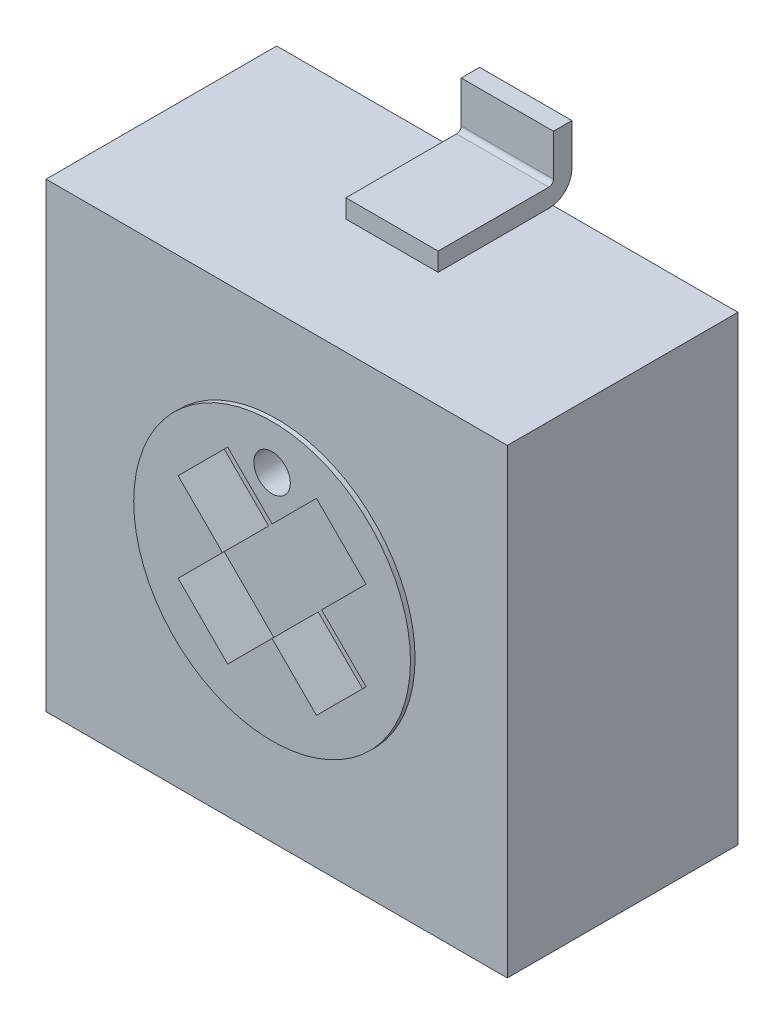
SolidWorks part; units mm, degrees
ref_plane "Front Plane" through (0, 0, 0) normal (0, 0, 1) x (1, 0, 0)
ref_plane "Top Plane" through (0, 0, 0) normal (0, 1, 0) x (1, 0, 0)
ref_plane "Right Plane" through (0, 0, 0) normal (1, 0, 0) x (0, 0, -1)
sketch "Sketch1" plane through (0, 0, 0) normal (0, 0, 1) x (1, 0, 0)
  line L1 (0, 0) -> (5, 0)
  line L2 (0, 0) -> (0, 5)
  line L3 (0, 5) -> (5, 5)
  line L4 (5, 0) -> (5, 5)
  dimension "D1" = 5
  dimension "D2" = 5
extrude "Boss-Extrude1" add sketch "Sketch1" along normal blind 2.5
ref_plane "Plane1" through (2.5, 0, 0) normal (1, 0, 0) x (0, 0, -1)
ref_plane "Plane2" through (1.35, 0, 0) normal (1, 0, 0) x (0, 0, -1)
sketch "Sketch2" plane through (2.5, 0, 0) normal (1, 0, 0) x (0, 0, -1)
  line L0 (-1.25, 5) -> (0.2, 5)
  line L1 (-2.5, 5) -> (0, 5) construction
  line L2 (0.2, 5) -> (0.2, 5.7)
  line L3 (-2.5, 0) -> (-2.5, 5) construction
  dimension "D1" = 2.7
  dimension "D2" = 0.7
extrude "Extrude-Thin1" add sketch "Sketch2" along normal mid plane 1 thin thin type one direction reverse wall 0.2
sketch "Sketch3" plane through (1.35, 0, 0) normal (1, 0, 0) x (0, 0, -1)
  line L0 (-1.25, 0) -> (0.2, 0)
  line L1 (-2.5, 0) -> (0, 0) construction
  line L2 (0.2, 0) -> (0.2, -0.7)
  line L3 (-2.5, 0) -> (-2.5, 5) construction
  dimension "D1" = 2.7
  dimension "D2" = 0.7
extrude "Extrude-Thin2" add sketch "Sketch3" along normal mid plane 0.9 thin
pattern_linear "LPattern1" count 2 spacing 2.3 along (1, 0, 0) of "Extrude-Thin2"
sketch "Sketch4" plane through (0, 0, 2.5) normal (0, 0, 1) x (1, 0, 0)
  circle A0 centre (2.5, 2.5) radius 1.5
  dimension "D1" = 3
extrude "Boss-Extrude2" add sketch "Sketch4" along normal blind 0.05
sketch "Sketch5" plane through (0, 0, 2.55) normal (0, 0, 1) x (1, 0, 0)
  line L0 (1, 2.5) -> (4, 2.5) construction
  line L1 (4, 2.5) -> (2.5, 4) construction
  line L2 (2.5, 4) -> (2.5, 1) construction
  line L3 (2.5, 1) -> (4, 2.5) construction
  line L4 (3.5607, 1.4393) -> (1.4393, 3.5607) construction
  line L5 (2.5, 4) -> (1, 2.5) construction
  line L6 (3.5607, 3.5607) -> (1.4393, 1.4393) construction
  line L7 (1, 2.5) -> (2.5, 1) construction
  line L8 (1.75, 3.25) -> (3.25, 1.75) construction
  line L9 (2.0187, 3.5187) -> (2.5, 3.0374)
  line L10 (3.25, 3.25) -> (1.75, 1.75) construction
  line L11 (1.75, 3.25) -> (3.25, 1.75) construction
  line L12 (1.4813, 2.9813) -> (1.9626, 2.5)
  line L13 (3.5187, 2.9813) -> (3.0374, 2.5)
  line L14 (3.25, 3.25) -> (1.75, 1.75) construction
  line L15 (2.9813, 3.5187) -> (2.5, 3.0374)
  line L16 (2.9813, 3.5187) -> (3.5187, 2.9813)
  line L17 (3.5187, 2.0187) -> (2.9813, 1.4813)
  line L18 (2.0187, 1.4813) -> (1.4813, 2.0187)
  line L19 (1.4813, 2.9813) -> (2.0187, 3.5187)
  line L20 (1.9626, 2.5) -> (1.4813, 2.0187)
  line L21 (3.0374, 2.5) -> (3.5187, 2.0187)
  line L22 (2.5, 1.9626) -> (2.0187, 1.4813)
  line L23 (2.5, 1.9626) -> (2.9813, 1.4813)
  circle A0 centre (2.5, 2.5) radius 1.5 construction
  circle A1 centre (2.5, 2.5) radius 1.5 construction
  circle A2 centre (2.5, 3.5187) radius 0.1977
  dimension "D2" = 2
  dimension "D1" = 2
  dimension "D4" = 2
  dimension "D3" = 2
extrude "Cut-Extrude2" cut sketch "Sketch5" against normal blind 0.5
